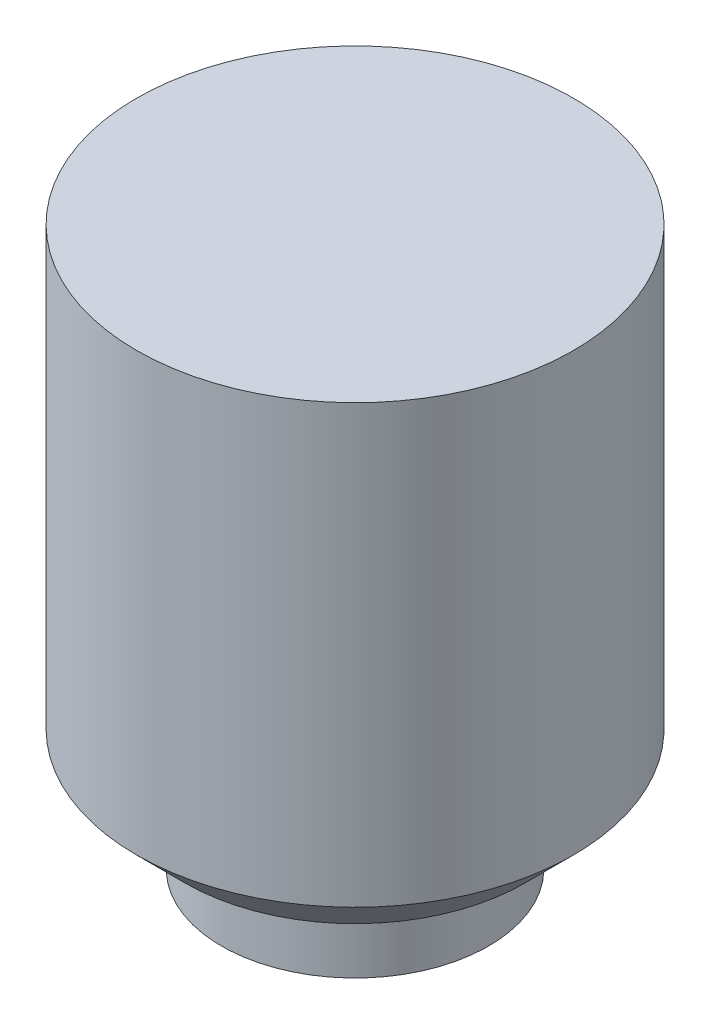
SolidWorks part; units mm, degrees
ref_plane "Front Plane" through (0, 0, 0) normal (0, 0, 1) x (1, 0, 0)
ref_plane "Top Plane" through (0, 0, 0) normal (0, 1, 0) x (1, 0, 0)
ref_plane "Right Plane" through (0, 0, 0) normal (1, 0, 0) x (0, 0, -1)
sketch "Sketch1" plane through (0, 0, 0) normal (0, 1, 0) x (1, 0, 0)
  circle A1 centre (0, 0) radius 4.5
  dimension "D1" = 9
extrude "Boss-Extrude1" add sketch "Sketch1" along normal blind 10
sketch "Sketch2" plane through (0, 0, 0) normal (0, -1, 0) x (1, 0, 0)
  line L0 (-1, 1.05) -> (1, 1.05)
  arc A0 (-1, 1.05) -> (1, 1.05) centre (0, 0) ccw
  dimension "D1" = 2.9
  dimension "D2" = 2
extrude "Cut-Extrude1" cut sketch "Sketch2" against normal blind 3
sketch "Sketch3" plane through (0, 0, 0) normal (0, -1, 0) x (1, 0, 0)
  circle A0 centre (0, 0) radius 1.75
  circle A1 centre (0, 0) radius 2.75
  dimension "D1" = 5.5
  dimension "D2" = 3.5
extrude "Boss-Extrude2" add sketch "Sketch3" along normal blind 1.5
chamfer "Chamfer1" distance 1 angle 45 1 edges at (0, 0, 4.5)
